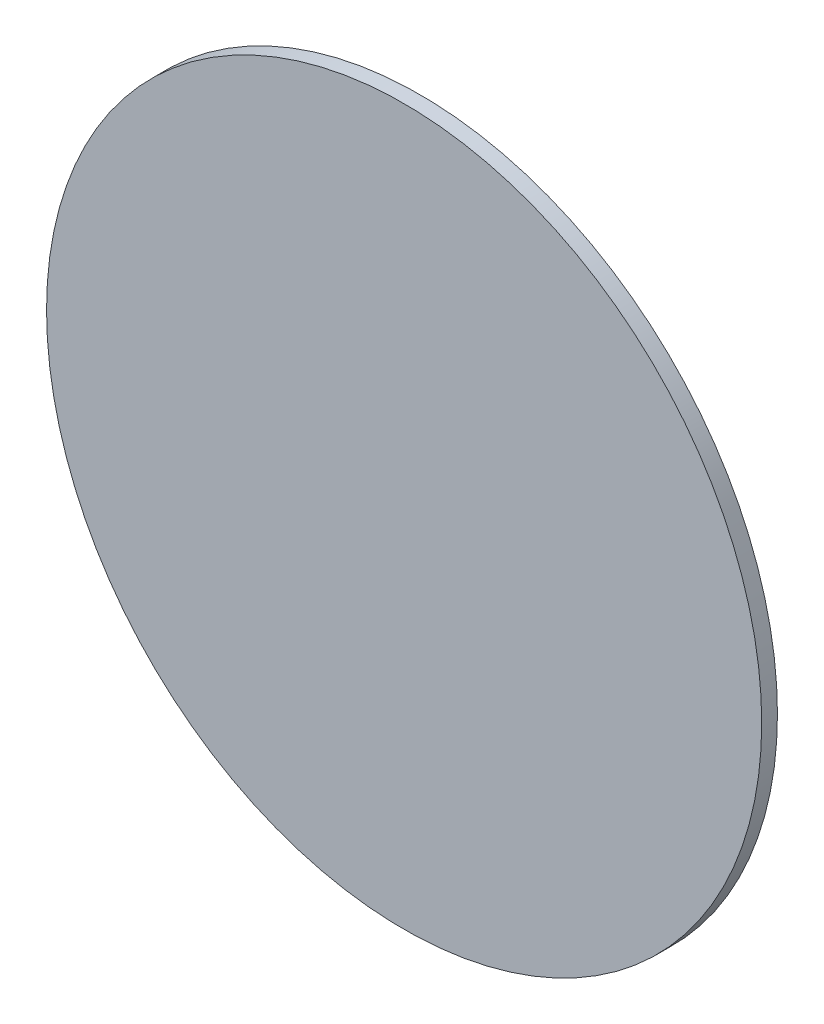
SolidWorks part; units mm, degrees
ref_plane "前视基准面" through (0, 0, 0) normal (0, 0, 1) x (1, 0, 0)
ref_plane "上视基准面" through (0, 0, 0) normal (0, 1, 0) x (1, 0, 0)
ref_plane "右视基准面" through (0, 0, 0) normal (1, 0, 0) x (0, 0, -1)
sketch "草图1" plane through (0, 0, 0) normal (0, 0, 1) x (1, 0, 0)
  circle A0 centre (0, 0) radius 25
  dimension "D1" = 50
extrude "凸台-拉伸1" add sketch "草图1" along normal blind 1.1
